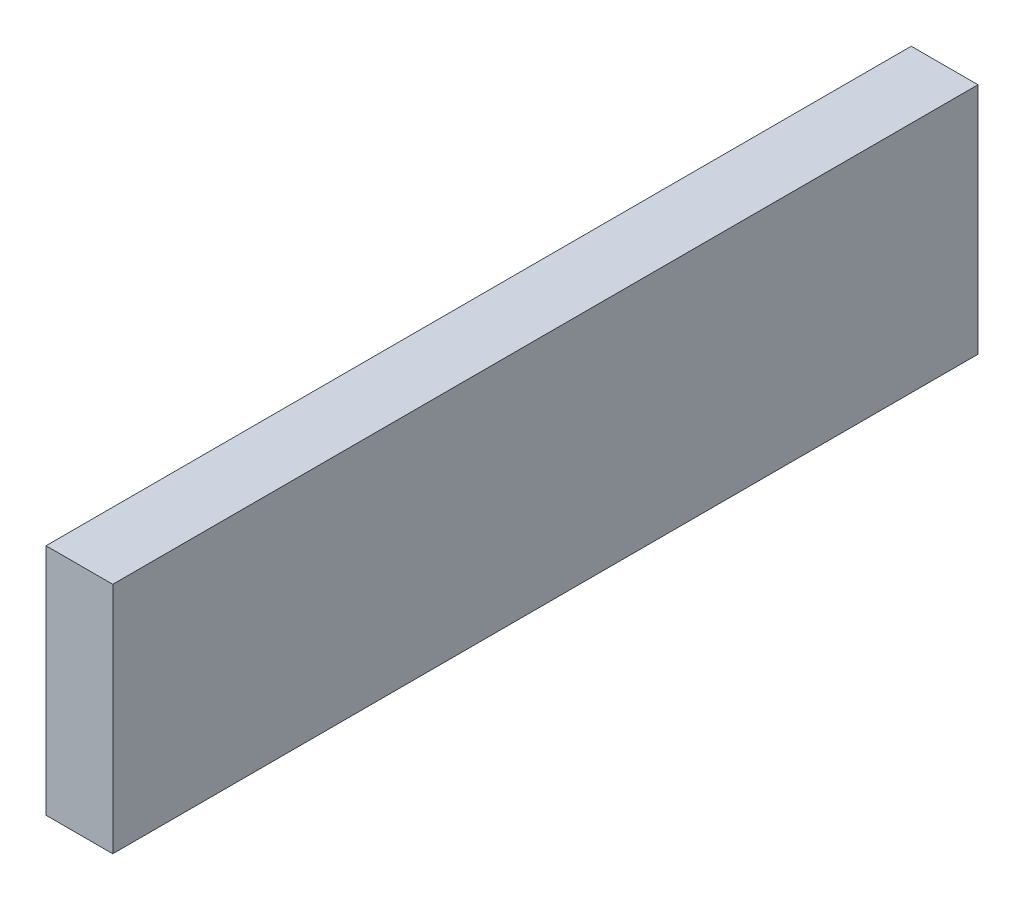
SolidWorks part; units mm, degrees
ref_plane "Front Plane" through (0, 0, 0) normal (0, 0, 1) x (1, 0, 0)
ref_plane "Top Plane" through (0, 0, 0) normal (0, 1, 0) x (1, 0, 0)
ref_plane "Right Plane" through (0, 0, 0) normal (1, 0, 0) x (0, 0, -1)
sketch "Sketch1" plane through (0, 0, 0) normal (1, 0, 0) x (0, 0, -1)
  line L0 (0, 0) -> (16.2, 0)
  line L1 (16.2, 0) -> (16.2, 17.8)
  line L2 (16.2, 17.8) -> (15.6, 17.8)
  line L3 (15.6, 17.8) -> (15.6, 3.97)
  line L4 (15.6, 3.97) -> (0.6, 3.97)
  line L5 (0.6, 3.97) -> (0.6, 17.8)
  line L6 (0.6, 17.8) -> (0, 17.8)
  line L7 (0, 17.8) -> (0, 0)
  dimension "D1" = 3.97
  dimension "D2" = 0.6
  dimension "D3" = 0.6
  dimension "D4" = 17.8
  dimension "D5" = 16.2
extrude "Boss-Extrude1" add sketch "Sketch1" along normal blind 1.25
sketch "Sketch2" plane through (1.25, 0, 0) normal (1, 0, 0) x (0, 0, -1)
  line L0 (16.2, 0) -> (16.2, 17.8) construction
  line L1 (16.2, 3.97) -> (0, 3.97)
  line L2 (16.2, 3.97) -> (16.2, 17.8)
  line L3 (16.2, 17.8) -> (0, 17.8)
  line L4 (0, 3.97) -> (0, 17.8)
extrude "Cut-Extrude1" cut sketch "Sketch2" against normal blind 1.25
sketch "Sketch3" plane through (0, 3.97, 0) normal (0, 1, 0) x (1, 0, 0)
  line L4 (0, 16.2) -> (0, 0)
  line L5 (0, 0) -> (1.25, 0)
  line L6 (1.25, 0) -> (1.25, 16.2)
  line L7 (1.25, 16.2) -> (0, 16.2)
  line L8 (0, 16.2) -> (0, 0)
  line L9 (0, 0) -> (1.25, 0)
  line L10 (1.25, 0) -> (1.25, 16.2)
  line L11 (1.25, 16.2) -> (0, 16.2)
  dimension "D1" = 0
extrude "Boss-Extrude2" add sketch "Sketch3" along normal blind 0.4
